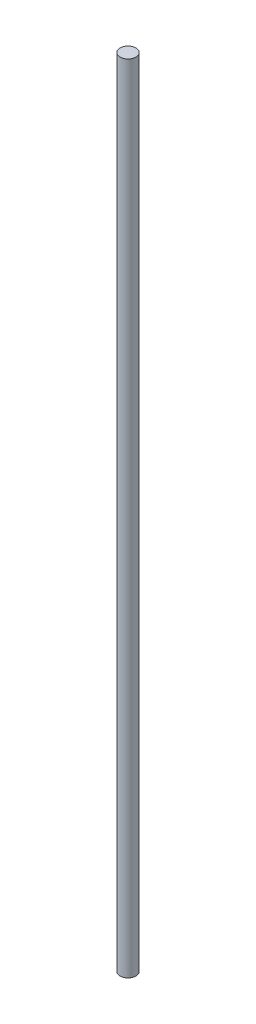
SolidWorks part; units mm, degrees
ref_plane "Front Plane" through (0, 0, 0) normal (0, 0, 1) x (1, 0, 0)
ref_plane "Top Plane" through (0, 0, 0) normal (0, 1, 0) x (1, 0, 0)
ref_plane "Right Plane" through (0, 0, 0) normal (1, 0, 0) x (0, 0, -1)
sketch "Sketch1" plane through (0, 0, 0) normal (0, 1, 0) x (1, 0, 0)
  circle A0 centre (0, 0) radius 4
extrude "Boss-Extrude1" add sketch "Sketch1" along normal blind 400
